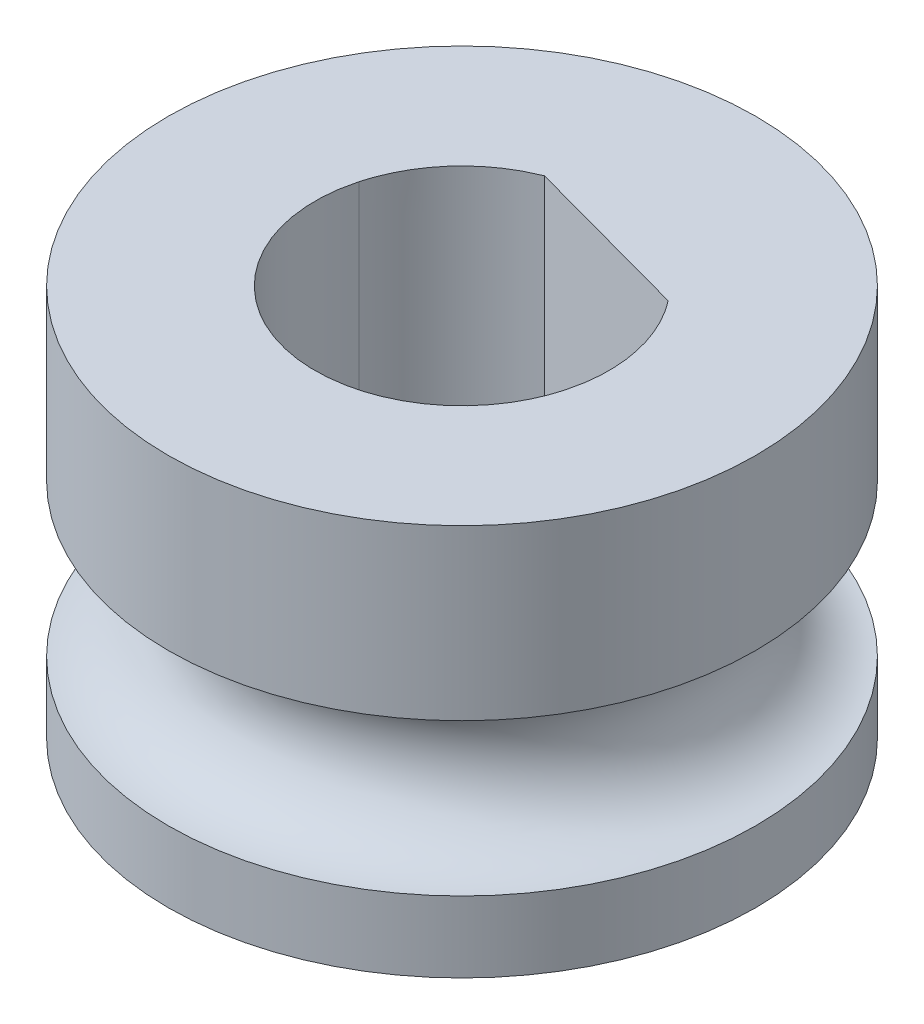
SolidWorks part; units mm, degrees
ref_plane "Front Plane" through (0, 0, 0) normal (0, 0, 1) x (1, 0, 0)
ref_plane "Top Plane" through (0, 0, 0) normal (0, 1, 0) x (1, 0, 0)
ref_plane "Right Plane" through (0, 0, 0) normal (1, 0, 0) x (0, 0, -1)
sketch "Sketch1" plane through (0, 0, 0) normal (0, 1, 0) x (1, 0, 0)
  circle A0 centre (0, 0) radius 6
  dimension "D1" = 12
extrude "Boss-Extrude1" add sketch "Sketch1" along normal blind 8
sketch "Sketch2" plane through (0, 0, 0) normal (0, 0, 1) x (1, 0, 0)
  line L0 (0, 0) -> (0, 8) construction
  line L1 (-6, 0) -> (6, 0) construction
  line L2 (6, 8) -> (-6, 8) construction
  line L3 (0, 3) -> (6, 3) construction
  line L4 (6, 0) -> (6, 8) construction
  circle A0 centre (6, 3) radius 1.55
  dimension "D2" = 3.1
  dimension "D1" = 3
revolve "Cut-Revolve1" cut sketch "Sketch2" angle 360 about L0
sketch "Sketch4" plane through (0, 8, 0) normal (0, 1, 0) x (1, 0, 0)
  line L0 (0.6312, 2.3155) -> (-0.789, -2.8944) construction
  line L1 (2.3678, 1.8421) -> (-1.1054, 2.7889)
  line L2 (-2.8944, 0.789) -> (2.8944, -0.789) construction
  spline S0 degree 3 poles (-2.8944, 0.789) (-2.9177, 0.6931) (-2.9642, 0.5022) (-2.9978, 0.2095) (-3.0041, -0.0848) (-2.973, -0.4765) (-2.8644, -0.9586) (-2.6209, -1.498) (-2.2795, -1.9817) (-1.8481, -2.387) (-1.3476, -2.7031) (-0.7939, -2.9125) (-0.2106, -3.0131) (0.3811, -2.9946) (0.9585, -2.8643) (1.4981, -2.6208) (1.9816, -2.2796) (2.291, -1.9501) (2.4733, -1.7009) (2.5651, -1.5595) (2.6483, -1.4139) (2.7231, -1.264) (2.7892, -1.1098) (2.8473, -0.9516) (2.8787, -0.8433) (2.8944, -0.789) knots 0 0 0 0 0.031431 0.062556 0.09368 0.125109 0.187591 0.250067 0.312549 0.375025 0.437507 0.499983 0.562465 0.624941 0.687423 0.749899 0.812381 0.874857 0.892877 0.910756 0.928548 0.946311 0.964103 0.981981 1 1 1 1
  spline S1 degree 3 poles (2.8944, -0.789) (2.9212, -0.6762) (2.9747, -0.4505) (3.0044, -0.103) (2.997, 0.2451) (2.9482, 0.59) (2.8604, 0.9271) (2.7548, 1.1976) (2.6523, 1.4056) (2.5664, 1.5567) (2.4724, 1.703) (2.4027, 1.7957) (2.3678, 1.8421) knots 0 0 0 0 0.124991 0.249974 0.37497 0.499947 0.624943 0.749921 0.81255 0.874965 0.937378 1 1 1 1
  spline S2 degree 3 poles (-1.1054, 2.7889) (-1.2118, 2.7426) (-1.4245, 2.6501) (-1.7203, 2.4653) (-1.9942, 2.2506) (-2.2409, 2.0045) (-2.4579, 1.7321) (-2.611, 1.4853) (-2.7159, 1.2785) (-2.7852, 1.1191) (-2.8459, 0.9561) (-2.8782, 0.8448) (-2.8944, 0.789) knots 0 0 0 0 0.124991 0.249974 0.37497 0.499947 0.624943 0.749921 0.81255 0.874965 0.937378 1 1 1 1
  point P6 (0, 0)
extrude "Cut-Extrude1" cut sketch "Sketch4" against normal blind 8
